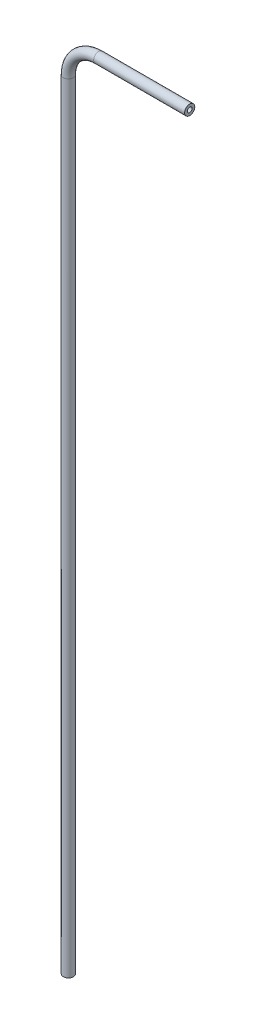
SolidWorks part; units mm, degrees
material "6061 Alloy"
ref_plane "Front Plane" through (0, 0, 0) normal (0, 0, 1) x (1, 0, 0)
ref_plane "Top Plane" through (0, 0, 0) normal (0, 1, 0) x (1, 0, 0)
ref_plane "Right Plane" through (0, 0, 0) normal (1, 0, 0) x (0, 0, -1)
sketch "Sketch1" plane through (0, 0, 0) normal (0, 0, 1) x (1, 0, 0)
  line L0 (0, -490.4723) -> (0, -1.5223)
  line L1 (19.05, 17.5277) -> (76.2, 17.5277)
  arc A0 (0, -1.5223) -> (19.05, 17.5277) centre (19.05, -1.5223) cw
  point P6 (0, 17.5277)
  dimension "D3" = 19.05
  dimension "D1" = 76.2
  dimension "D2" = 508
ref_plane "Plane1" through (76.2, 17.5277, 0) normal (1, 0, 0) x (0, 0, -1)
sketch "Sketch2" plane through (76.2, 17.5277, 0) normal (1, 0, 0) x (0, 0, -1)
  circle A0 centre (0, 0) radius 3.175
  circle A1 centre (0, 0) radius 1.524
  dimension "D1" = 6.35
  dimension "D2" = 3.048
sweep "Sweep1" add profiles "Sketch2" path "Sketch1"
